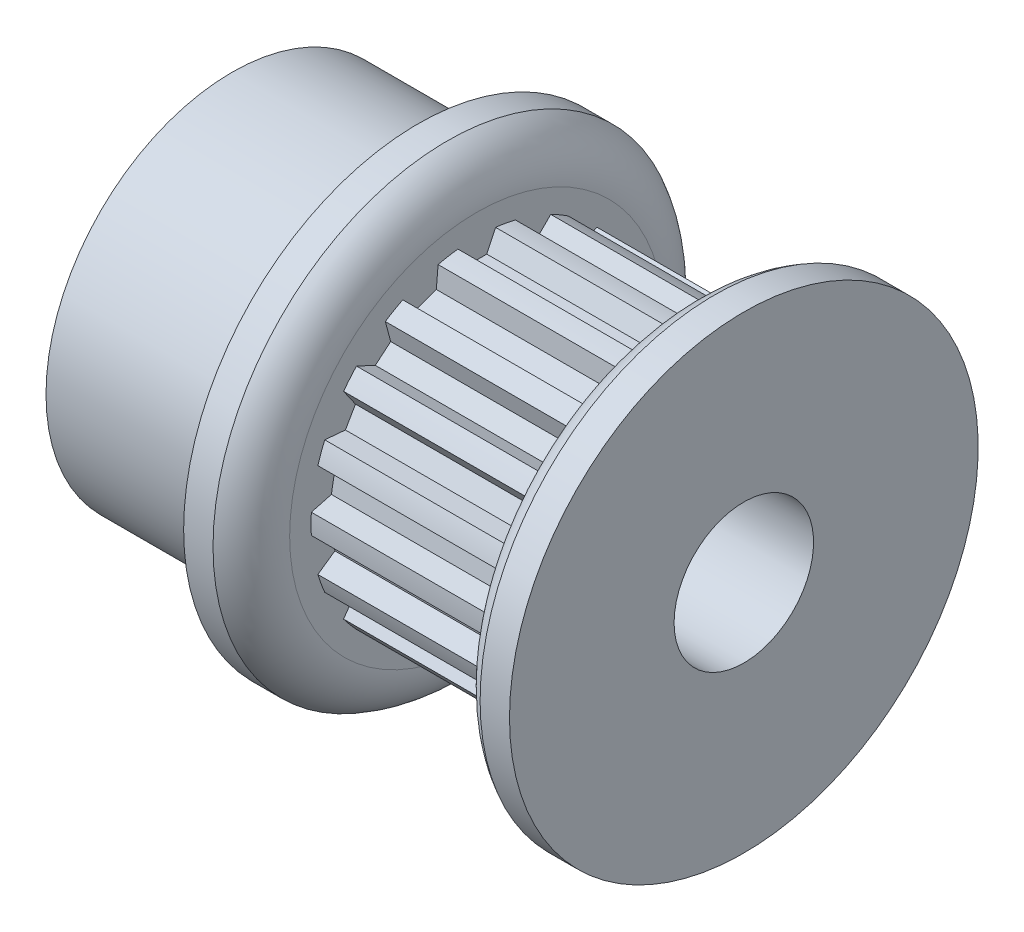
SolidWorks part; units mm, degrees
ref_plane "Front Plane" through (0, 0, 0) normal (0, 0, 1) x (1, 0, 0)
ref_plane "Top Plane" through (0, 0, 0) normal (0, 1, 0) x (1, 0, 0)
ref_plane "Right Plane" through (0, 0, 0) normal (1, 0, 0) x (0, 0, -1)
sketch "Sketch2" plane through (0, 0, 0) normal (1, 0, 0) x (0, 0, -1)
  line L3 (0, 0) -> (0, 4.9911) construction
  line L6 (0, -5.4991) -> (0, -5.8166) construction
  line L7 (-0.5715, 5.4693) -> (-0.343, 4.9793)
  line L8 (0.5715, 5.4693) -> (0.343, 4.9793)
  line L9 (-0.5715, 5.4693) -> (-0.6424, 5.6213)
  line L10 (0.5715, 5.4693) -> (0.6424, 5.6213)
  line L12 (-0.343, 4.9793) -> (0.343, 4.9793)
  line L14 (0, 5.4991) -> (0, 5.8166) construction
  line L15 (0, 0) -> (0, -1.143) construction
  circle A0 centre (0, 0) radius 5.8166 construction
  circle A1 centre (0, 0) radius 4.9911 construction
  circle A2 centre (0, 0) radius 5.4991 construction
  arc A7 (0.6424, 5.6213) -> (-0.6424, 5.6213) centre (0, 0) ccw
  point P5 (0, 5.6578)
  dimension "D3" = 0.3175
  dimension "D1" = 50
sketch "Sketch1" plane through (0, 0, 0) normal (0, 0, 1) x (1, 0, 0)
  line L0 (-8.7376, 0) -> (8.7376, 0) construction
  line L1 (-8.7376, 2.3813) -> (8.7376, 2.3813)
  line L2 (-8.7376, 2.3813) -> (-8.7376, 6.35)
  line L3 (-2.3876, 8.001) -> (-1.3843, 8.001)
  line L4 (-0.381, 5.8166) -> (-0.381, 6.3881)
  line L5 (-0.381, 6.9596) -> (-0.381, 5.8166) construction
  line L6 (-0.381, 5.8166) -> (6.731, 5.8166)
  line L7 (6.731, 5.8166) -> (6.731, 6.3881)
  line L8 (6.731, 5.8166) -> (8.7376, 5.8166) construction
  line L9 (7.7343, 8.001) -> (8.7376, 8.001)
  line L10 (8.7376, 8.001) -> (8.7376, 2.3813)
  line L11 (7.7343, 5.8166) -> (7.7343, 8.001) construction
  line L12 (-5.5626, 6.35) -> (-5.5626, 2.3812) construction
  line L13 (-2.3876, 8.001) -> (-2.3876, 6.35)
  line L14 (-2.3876, 6.35) -> (-8.7376, 6.35)
  arc A0 (6.731, 6.3881) -> (7.7343, 8.001) centre (8.5291, 6.3881) cw
  arc A1 (-0.381, 6.3881) -> (-1.3843, 8.001) centre (-2.1791, 6.3881) ccw
  dimension "Bore Size" = 4.7625
  dimension "Overall Width" = 17.4752
  dimension "Inside Width" = 7.112
  dimension "OD" = 16.002
  dimension "D2" = 11.6332
  dimension "D3" = 1.143
  dimension "D4" = 0.5715
  dimension "Outside Width" = 11.1252
revolve "Revolve1" add sketch "Sketch1" angle 360 mid plane about L0
sketch "Sketch4" plane through (-0.381, 0, 0) normal (1, 0, 0) x (0, 0, -1)
  circle A0 centre (0, 0) radius 5.6578
  circle A2 centre (0, 0) radius 5.8166
  circle A3 centre (0, 0) radius 5.8166 construction
extrude "Cut-Extrude2" cut sketch "Sketch4" along normal up to surface (7.112 mm away) up to face at (6.731, 0, 5.8166)
sketch "Sketch3" plane through (-0.381, 0, 0) normal (1, 0, 0) x (0, 0, -1)
  line L2 (-0.5715, 5.4693) -> (-0.343, 4.9793) construction
  line L3 (-0.343, 4.9793) -> (0.343, 4.9793) construction
  line L4 (0.5715, 5.4693) -> (0.343, 4.9793) construction
  line L5 (-0.6424, 5.6213) -> (-0.343, 4.9793)
  line L6 (-0.343, 4.9793) -> (0.343, 4.9793)
  line L7 (0.6424, 5.6213) -> (0.343, 4.9793)
  arc A1 (0.6424, 5.6213) -> (-0.6424, 5.6213) centre (0, 0) ccw construction
  arc A2 (0.6424, 5.6213) -> (-0.6424, 5.6213) centre (0, 0) ccw
extrude "Cut-Extrude1" cut sketch "Sketch3" along normal up to surface (7.112 mm away) up to face at (6.731, 0, 6.3881)
pattern_circular "CirPattern1" count 18 over 360 about axis through (0, 0, 0) along (1, 0, 0) of "Cut-Extrude1"
sketch "Sketch5" plane through (0, 0, 0) normal (0, 0, 1) x (1, 0, 0)
  line L1 (6.731, 6.3881) -> (6.731, -6.3881) construction
  point P0 (6.731, 0)
equation "\"D3@Sketch2\" = (\"hs@Sketch2\"-\"ht@Sketch2\")/2"
equation "\"D2@Sketch1\" = \"PD@Sketch2\""
equation "\"D3@Sketch1\" = \"hs@Sketch2\""
equation "\"D4@Sketch1\" = \"D3@Sketch1\"/2"
